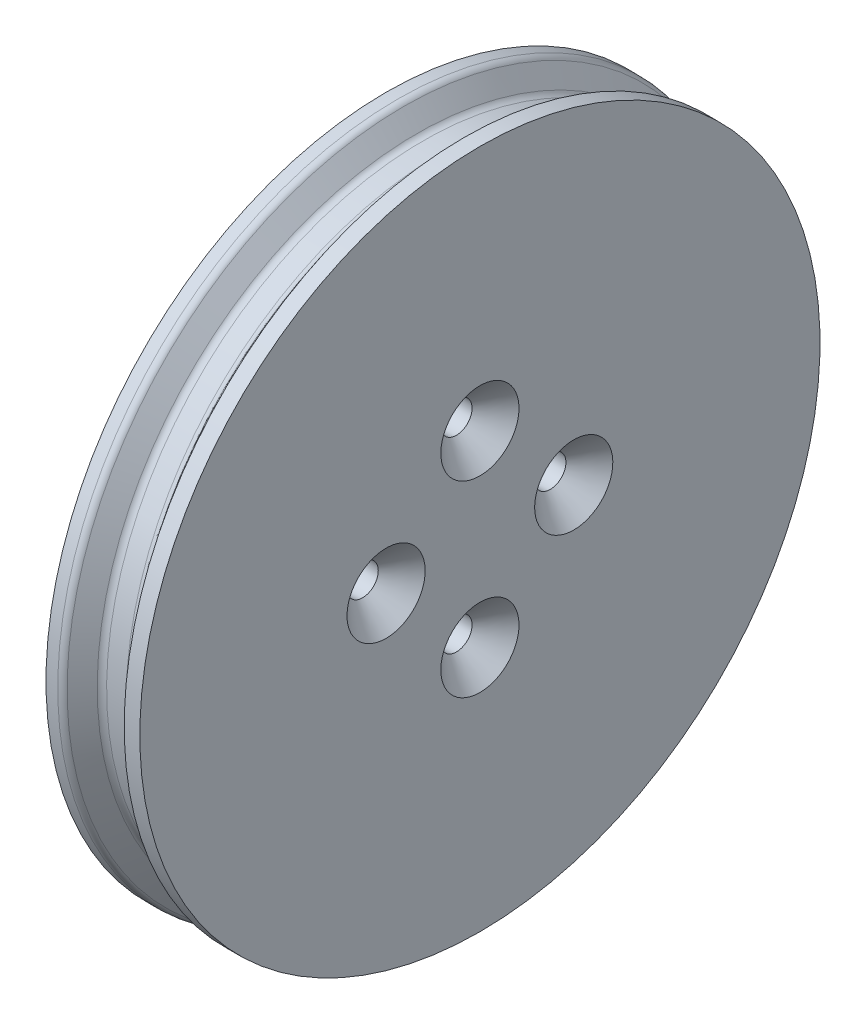
SolidWorks part; units mm, degrees
ref_plane "Piano frontale" through (0, 0, 0) normal (0, 0, 1) x (1, 0, 0)
ref_plane "Piano superiore" through (0, 0, 0) normal (0, 1, 0) x (1, 0, 0)
ref_plane "Piano destro" through (0, 0, 0) normal (1, 0, 0) x (0, 0, -1)
sketch "Schizzo1" plane through (0, 0, 0) normal (0, 0, 1) x (1, 0, 0)
  line L0 (0, 0) -> (0, 17.3)
  line L1 (0, 17.3) -> (-3, 17.3)
  line L2 (-3, 17.3) -> (-3, 21.75)
  line L6 (3, 21.75) -> (3, 0)
  line L7 (3, 0) -> (0, 0) construction
  line L9 (0, 0) -> (3, 0)
  line L10 (-0.875, 20.25) -> (0.875, 20.25)
  line L11 (0.875, 20.25) -> (2, 21.75)
  line L17 (2, 21.75) -> (3, 21.75)
  line L18 (-3, 21.75) -> (-2, 21.75)
  line L19 (-2, 21.75) -> (-0.875, 20.25)
  line L22 (0, 20.25) -> (0, 22) construction
  circle A0 centre (0, 22) radius 1.75 construction
  point P3 (3, 21.7091)
  point P11 (0.6654, 22)
  point P12 (-1.7739, 29.2647)
  point P13 (-1.5901, 29.2987)
  point P14 (3, 21.0947)
  point P15 (1.2372, 29.25)
  point P16 (-2, 30.0333)
  point P17 (3, 30.0333)
  point P21 (0.5, 23.6369)
  point P22 (-2, 21.0698)
  point P23 (3, 21.0883)
  point P24 (1.3202, 20.25)
  point P25 (3, 21.0689)
  point P27 (2, 21.0947)
  point P28 (0.9774, 20.25)
  dimension "D4" = 3.5
  dimension "D1" = 34.6
  dimension "D2" = 3
  dimension "D3" = 6
  dimension "D5" = 1
  dimension "D6" = 1.5
  dimension "D8" = 22
revolve "Rivoluzione1" add sketch "Schizzo1" angle 360 about L9
sketch "Schizzo2" plane through (3, 0, 0) normal (1, 0, 0) x (0, 0, -1)
  line L0 (0, 0) -> (0, 6) construction
  circle A0 centre (0, 6) radius 1
  circle A1 centre (6, 0) radius 1
  circle A2 centre (0, -6) radius 1
  circle A3 centre (-6, 0) radius 1
  point P13 (0, 0)
  dimension "D1" = 2
  dimension "D3" = 12
  dimension "D2" = 4
extrude "Taglio-Estrusione1" cut sketch "Schizzo2" against normal blind 10
chamfer "Smusso1" distance 1.5 angle 45 4 edges at (3, 1, -6) (3, -5, 0) (3, 1, 6) (3, 7, 0)
fillet "Raccordo1" radius 0.5 3 edges at (0.875, -20.25, 0) (-0.875, -20.25, 0) (-2, -21.75, 0)
